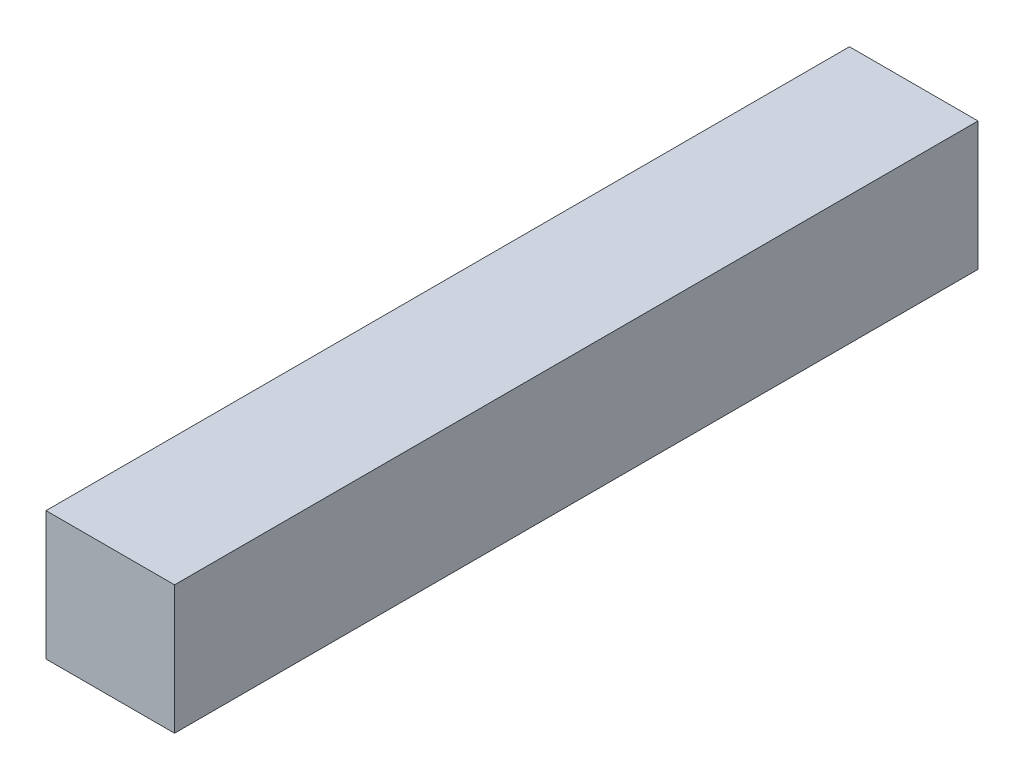
SolidWorks part; units mm, degrees
ref_plane "Front Plane" through (0, 0, 0) normal (0, 0, 1) x (1, 0, 0)
ref_plane "Top Plane" through (0, 0, 0) normal (0, 1, 0) x (1, 0, 0)
ref_plane "Right Plane" through (0, 0, 0) normal (1, 0, 0) x (0, 0, -1)
sketch "Sketch1" plane through (0, 0, 0) normal (0, 1, 0) x (1, 0, 0)
  line L1 (1, -6.25) -> (-1, -6.25)
  line L2 (1, -6.25) -> (1, 6.25)
  line L3 (1, 6.25) -> (-1, 6.25)
  line L4 (-1, -6.25) -> (-1, 6.25)
  line L5 (1, -6.25) -> (-1, 6.25) construction
  line L6 (1, 6.25) -> (-1, -6.25) construction
  point P0 (0, 0)
  dimension "D1" = 12.5
  dimension "D2" = 2
extrude "Boss-Extrude1" add sketch "Sketch1" along normal blind 2
